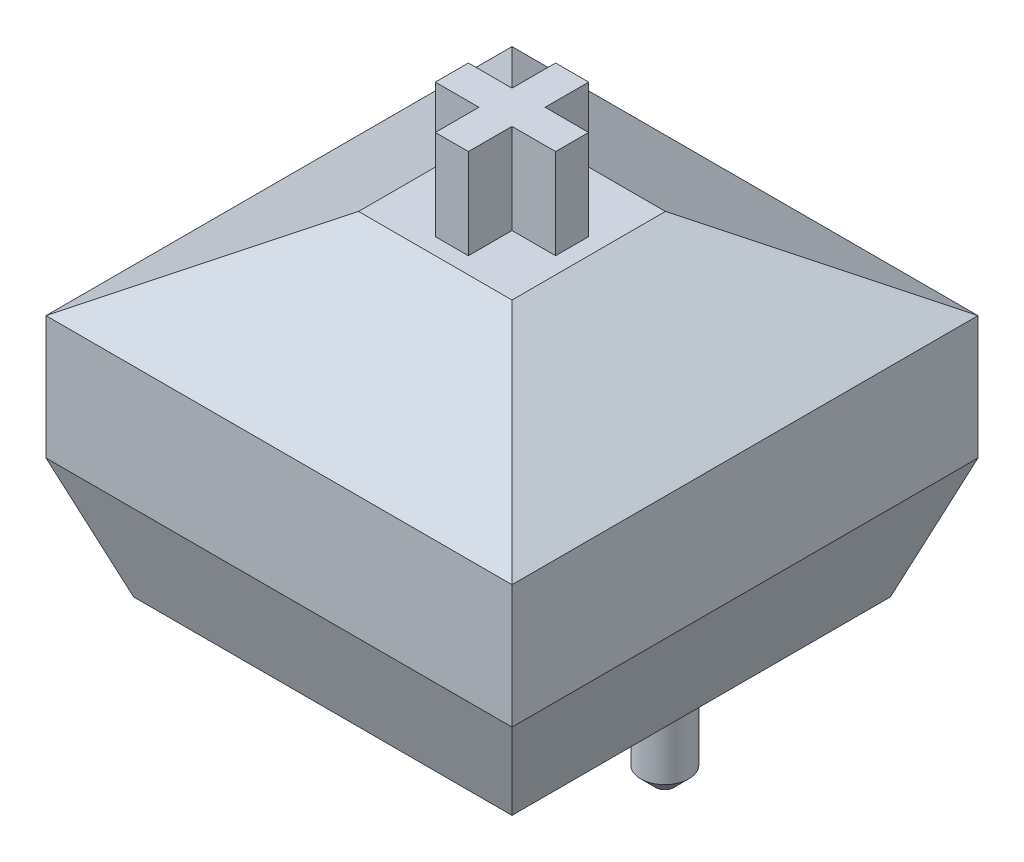
SolidWorks part; units mm, degrees
ref_plane "Front Plane" through (0, 0, 0) normal (0, 0, 1) x (1, 0, 0)
ref_plane "Top Plane" through (0, 0, 0) normal (0, 1, 0) x (1, 0, 0)
ref_plane "Right Plane" through (0, 0, 0) normal (1, 0, 0) x (0, 0, -1)
sketch "Sketch1" plane through (0, 0, 0) normal (0, 1, 0) x (1, 0, 0)
  circle A0 centre (0, 0) radius 1.9
  circle A1 centre (5.08, 0) radius 0.8
  circle A2 centre (-5.08, 0) radius 0.8
  circle A3 centre (-3.81, 2.54) radius 0.6
  circle A4 centre (2.54, 5.08) radius 0.6
  dimension "D1" = 3.8
  dimension "D2" = 1.6
  dimension "D5" = 1.2
  dimension "D3" = 5.08
  dimension "D4" = 5.08
  dimension "D6" = 3.81
  dimension "D7" = 2.54
  dimension "D8" = 5.08
  dimension "D9" = 2.54
extrude "Boss-Extrude1" add sketch "Sketch1" against normal blind 2.8
sketch "Sketch2" plane through (0, 0, 0) normal (0, 1, 0) x (1, 0, 0)
  line L1 (7.747, -7.747) -> (-7.747, -7.747)
  line L2 (7.747, -7.747) -> (7.747, 7.747)
  line L3 (7.747, 7.747) -> (-7.747, 7.747)
  line L4 (-7.747, -7.747) -> (-7.747, 7.747)
  line L5 (7.747, -7.747) -> (-7.747, 7.747) construction
  line L6 (7.747, 7.747) -> (-7.747, -7.747) construction
  point P0 (0, 0)
  dimension "D1" = 15.494
extrude "Boss-Extrude2" add sketch "Sketch2" along normal blind 11.1
sketch "Sketch3" plane through (0, 11.1, 0) normal (0, 1, 0) x (-1, 0, 0)
  line L0 (-0.55, 0.1512) -> (-0.55, 0.55) construction
  line L1 (0.55, -2) -> (-0.55, -2)
  line L2 (0.55, -2) -> (0.55, -0.55)
  line L3 (0.55, 2) -> (-0.55, 2)
  line L4 (-0.55, -2) -> (-0.55, -0.55)
  line L5 (0.55, -2) -> (0.1512, -0.55) construction
  line L6 (0.55, 2) -> (0.1512, 0.55) construction
  line L7 (-2, -0.55) -> (-0.55, -0.55)
  line L8 (-2, -0.55) -> (-2, 0.55)
  line L9 (-2, 0.55) -> (-0.55, 0.55)
  line L10 (2, -0.55) -> (2, 0.55)
  line L11 (-2, -0.55) -> (0, 0) construction
  line L12 (-2, 0.55) -> (0, 0) construction
  line L13 (-0.55, 0.55) -> (-0.55, 2)
  line L14 (0, 0) -> (-0.1513, 0.55) construction
  line L15 (-0.1513, 0.55) -> (-0.55, 2) construction
  line L16 (0.1512, 0.55) -> (0, 0) construction
  line L17 (-0.1513, -0.55) -> (-0.55, -2) construction
  line L18 (0.55, 0.1512) -> (0.55, 0.55) construction
  line L19 (0.55, 0.55) -> (0.55, 2)
  line L20 (0.55, -0.55) -> (0.55, -0.1513) construction
  line L21 (0.55, -0.1513) -> (0.55, 0.1512) construction
  line L22 (0.1512, -0.55) -> (0, 0) construction
  line L23 (0, 0) -> (-0.1513, -0.55) construction
  line L24 (-0.55, -0.55) -> (-0.55, -0.1513) construction
  line L25 (-0.55, -0.1513) -> (-0.55, 0.1512) construction
  line L26 (-0.55, -0.55) -> (-0.1513, -0.55) construction
  line L27 (-0.1513, -0.55) -> (0.1512, -0.55) construction
  line L28 (0.1512, -0.55) -> (0.55, -0.55) construction
  line L29 (0.55, -0.55) -> (2, -0.55)
  line L30 (0, 0) -> (0.55, -0.1513) construction
  line L31 (0.55, -0.1513) -> (2, -0.55) construction
  line L32 (0, 0) -> (0.55, 0.1512) construction
  line L33 (0.55, 0.1512) -> (2, 0.55) construction
  line L34 (0.1512, 0.55) -> (0.55, 0.55) construction
  line L35 (0.55, 0.55) -> (2, 0.55)
  line L36 (-0.55, 0.55) -> (-0.1513, 0.55) construction
  line L37 (-0.1513, 0.55) -> (0.1512, 0.55) construction
  point P0 (0, 0)
  point P6 (0, 0)
  dimension "D1" = 4
  dimension "D2" = 1.1
extrude "Boss-Extrude3" add sketch "Sketch3" along normal blind 3
chamfer "Chamfer1" distance 3 angle 60 4 edges at (0, 11.1, -7.747) (7.747, 11.1, 0) (0, 11.1, 7.747) (-7.747, 11.1, 0)
chamfer "Chamfer2" distance 4 angle 20 4 edges at (-7.747, 0, 0) (0, 0, 7.747) (7.747, 0, 0) (0, 0, -7.747)
chamfer "Chamfer3" distance 0.5 angle 45 3 edges at (0, -2.8, 1.9) (-5.08, -2.8, 0.8) (5.08, -2.8, 0.8)
equation "\"D4@Sketch1\"=\"D3@Sketch1\""
